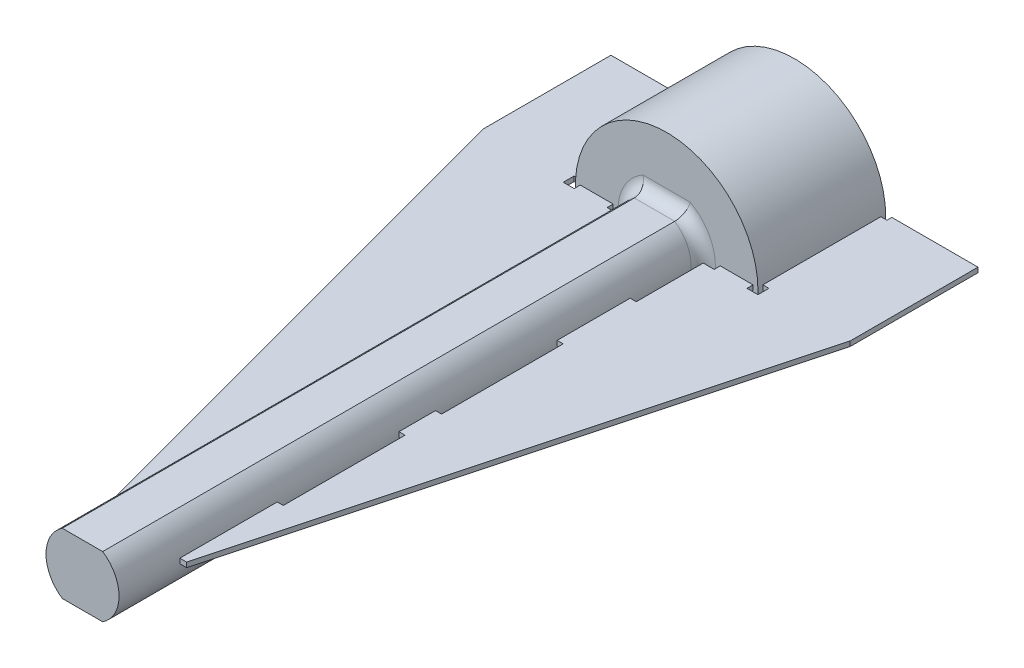
SolidWorks part; units mm, degrees
ref_plane "Front Plane" through (0, 0, 0) normal (0, 0, 1) x (1, 0, 0)
ref_plane "Top Plane" through (0, 0, 0) normal (0, 1, 0) x (1, 0, 0)
ref_plane "Right Plane" through (0, 0, 0) normal (1, 0, 0) x (0, 0, -1)
sketch "Sketch2" plane through (0, 0, 0) normal (0, 0, 1) x (1, 0, 0)
  arc A0 (-181.5583, 16.7096) -> (-181.559, 16.708) centre (-180.7258, 16.3677) ccw
  arc A1 (-181.559, 16.708) -> (-181.7515, 15.4803) centre (-179.0594, 15.6871) ccw
  arc A2 (-181.7515, 15.4803) -> (-180.9711, 14.942) centre (-178.5779, 19.2465) ccw
  arc A3 (-180.9711, 14.942) -> (-179.8919, 15.5581) centre (-181.7341, 17.532) ccw
  arc A4 (-179.8919, 15.5581) -> (-179.8906, 15.5593) centre (-180.506, 16.216) ccw
  arc A5 (-179.8906, 15.5593) -> (-179.8906, 15.5593) centre (-179.8906, 15.5593) cw
  arc A6 (-179.8906, 15.5593) -> (-179.8906, 15.5593) centre (-179.8906, 15.5593) ccw
  arc A7 (-179.8906, 15.5593) -> (-179.8906, 15.5593) centre (-179.8906, 15.5593) cw
  arc A8 (-179.8906, 15.5593) -> (-179.8904, 15.5575) centre (-178.9987, 15.6794) ccw
  arc A9 (-179.8904, 15.5575) -> (-179.4433, 14.3981) centre (-177.2152, 15.9232) ccw
  arc A10 (-179.4433, 14.3981) -> (-178.4982, 14.3221) centre (-178.5779, 19.2465) ccw
  arc A11 (-178.4982, 14.3221) -> (-177.8717, 15.3952) centre (-180.454, 16.1836) ccw
  arc A12 (-177.8717, 15.3952) -> (-177.8711, 15.3969) centre (-178.7324, 15.658) ccw
  arc A13 (-177.8711, 15.3969) -> (-177.8711, 15.3969) centre (-177.8711, 15.3969) cw
  arc A14 (-177.8711, 15.3969) -> (-177.8711, 15.3969) centre (-177.8711, 15.3969) ccw
  arc A15 (-177.8711, 15.3969) -> (-177.8711, 15.3969) centre (-177.8711, 15.3969) cw
  arc A16 (-177.8711, 15.3969) -> (-177.87, 15.3955) centre (-177.1587, 15.9469) ccw
  arc A17 (-177.87, 15.3955) -> (-176.9031, 14.615) centre (-175.7362, 17.0498) ccw
  arc A18 (-176.9031, 14.615) -> (-176.0467, 15.0217) centre (-178.5779, 19.2465) ccw
  arc A19 (-176.0467, 15.0217) -> (-176.0406, 16.2643) centre (-178.6712, 15.6559) ccw
  arc A20 (-176.0406, 16.2643) -> (-176.0411, 16.2661) centre (-176.9175, 16.0615) ccw
  arc A21 (-176.0411, 16.2661) -> (-176.0411, 16.2661) centre (-176.0411, 16.2661) cw
  arc A22 (-176.0411, 16.2661) -> (-176.0411, 16.2661) centre (-176.0411, 16.2661) ccw
  arc A23 (-176.0411, 16.2661) -> (-176.0411, 16.2661) centre (-176.0411, 16.2661) cw
  arc A24 (-176.0411, 16.2661) -> (-176.0394, 16.2654) centre (-175.6991, 17.0986) ccw
  arc A25 (-176.0394, 16.2654) -> (-174.8118, 16.0729) centre (-175.0185, 18.765) ccw
  arc A26 (-174.8118, 16.0729) -> (-174.2735, 16.8533) centre (-178.5779, 19.2465) ccw
  arc A27 (-174.2735, 16.8533) -> (-174.8895, 17.9325) centre (-176.8634, 16.0903) ccw
  arc A28 (-174.8895, 17.9325) -> (-174.8907, 17.9338) centre (-175.5475, 17.3184) ccw
  arc A29 (-174.8907, 17.9338) -> (-174.8907, 17.9338) centre (-174.8907, 17.9338) cw
  arc A30 (-174.8907, 17.9338) -> (-174.8907, 17.9338) centre (-174.8907, 17.9338) ccw
  arc A31 (-174.8907, 17.9338) -> (-174.8907, 17.9338) centre (-174.8907, 17.9338) cw
  arc A32 (-174.8907, 17.9338) -> (-174.8889, 17.9341) centre (-175.0108, 18.8258) ccw
  arc A33 (-174.8889, 17.9341) -> (-173.7295, 18.3812) centre (-175.2546, 20.6092) ccw
  arc A34 (-173.7295, 18.3812) -> (-173.6536, 19.3262) centre (-178.5779, 19.2465) ccw
  arc A35 (-173.6536, 19.3262) -> (-174.7267, 19.9528) centre (-175.515, 17.3704) ccw
  arc A36 (-174.7267, 19.9528) -> (-174.7284, 19.9533) centre (-174.9894, 19.092) ccw
  arc A37 (-174.7284, 19.9533) -> (-174.7284, 19.9533) centre (-174.7284, 19.9533) cw
  arc A38 (-174.7284, 19.9533) -> (-174.7284, 19.9533) centre (-174.7284, 19.9533) ccw
  arc A39 (-174.7284, 19.9533) -> (-174.7284, 19.9533) centre (-174.7284, 19.9533) cw
  arc A40 (-174.7284, 19.9533) -> (-174.7269, 19.9544) centre (-175.2784, 20.6657) ccw
  arc A41 (-174.7269, 19.9544) -> (-173.9464, 20.9213) centre (-176.3812, 22.0882) ccw
  arc A42 (-173.9464, 20.9213) -> (-174.3531, 21.7777) centre (-178.5779, 19.2465) ccw
  arc A43 (-174.3531, 21.7777) -> (-175.5958, 21.7838) centre (-174.9873, 19.1532) ccw
  arc A44 (-175.5958, 21.7838) -> (-175.5975, 21.7834) centre (-175.3929, 20.9069) ccw
  arc A45 (-175.5975, 21.7834) -> (-175.5975, 21.7834) centre (-175.5975, 21.7834) cw
  arc A46 (-175.5975, 21.7834) -> (-175.5975, 21.7834) centre (-175.5975, 21.7834) ccw
  arc A47 (-175.5975, 21.7834) -> (-175.5975, 21.7834) centre (-175.5975, 21.7834) cw
  arc A48 (-175.5975, 21.7834) -> (-175.5968, 21.785) centre (-176.43, 22.1253) ccw
  arc A49 (-175.5968, 21.785) -> (-175.4043, 23.0126) centre (-178.0964, 22.8059) ccw
  arc A50 (-175.4043, 23.0126) -> (-176.1848, 23.551) centre (-178.5779, 19.2465) ccw
  arc A51 (-176.1848, 23.551) -> (-177.2639, 22.9349) centre (-175.4217, 20.961) ccw
  arc A52 (-177.2639, 22.9349) -> (-177.2652, 22.9337) centre (-176.6499, 22.277) ccw
  arc A53 (-177.2652, 22.9337) -> (-177.2652, 22.9337) centre (-177.2652, 22.9337) cw
  arc A54 (-177.2652, 22.9337) -> (-177.2652, 22.9337) centre (-177.2652, 22.9337) ccw
  arc A55 (-177.2652, 22.9337) -> (-177.2652, 22.9337) centre (-177.2652, 22.9337) cw
  arc A56 (-177.2652, 22.9337) -> (-177.2655, 22.9355) centre (-178.1572, 22.8136) ccw
  arc A57 (-177.2655, 22.9355) -> (-177.7126, 24.0949) centre (-179.9406, 22.5698) ccw
  arc A58 (-177.7126, 24.0949) -> (-178.6576, 24.1708) centre (-178.5779, 19.2465) ccw
  arc A59 (-178.6576, 24.1708) -> (-179.2842, 23.0978) centre (-176.7018, 22.3094) ccw
  arc A60 (-179.2842, 23.0978) -> (-179.2847, 23.096) centre (-178.4234, 22.835) ccw
  arc A61 (-179.2847, 23.096) -> (-179.2847, 23.096) centre (-179.2847, 23.096) cw
  arc A62 (-179.2847, 23.096) -> (-179.2847, 23.096) centre (-179.2847, 23.096) ccw
  arc A63 (-179.2847, 23.096) -> (-179.2847, 23.096) centre (-179.2847, 23.096) cw
  arc A64 (-179.2847, 23.096) -> (-179.2858, 23.0975) centre (-179.9971, 22.546) ccw
  arc A65 (-179.2858, 23.0975) -> (-180.2527, 23.878) centre (-181.4197, 21.4432) ccw
  arc A66 (-180.2527, 23.878) -> (-181.1091, 23.4713) centre (-178.5779, 19.2465) ccw
  arc A67 (-181.1091, 23.4713) -> (-181.1152, 22.2287) centre (-178.4846, 22.8371) ccw
  arc A68 (-181.1152, 22.2287) -> (-181.1148, 22.2269) centre (-180.2383, 22.4315) ccw
  arc A69 (-181.1148, 22.2269) -> (-181.1148, 22.2269) centre (-181.1148, 22.2269) cw
  arc A70 (-181.1148, 22.2269) -> (-181.1148, 22.2269) centre (-181.1148, 22.2269) ccw
  arc A71 (-181.1148, 22.2269) -> (-181.1148, 22.2269) centre (-181.1148, 22.2269) cw
  arc A72 (-181.1148, 22.2269) -> (-181.1165, 22.2276) centre (-181.4567, 21.3944) ccw
  arc A73 (-181.1165, 22.2276) -> (-182.3441, 22.4201) centre (-182.1373, 19.728) ccw
  arc A74 (-182.3441, 22.4201) -> (-182.8824, 21.6397) centre (-178.5779, 19.2465) ccw
  arc A75 (-182.8824, 21.6397) -> (-182.2664, 20.5605) centre (-180.2924, 22.4027) ccw
  arc A76 (-182.2664, 20.5605) -> (-182.2651, 20.5592) centre (-181.6084, 21.1746) ccw
  arc A77 (-182.2651, 20.5592) -> (-182.2651, 20.5592) centre (-182.2651, 20.5592) cw
  arc A78 (-182.2651, 20.5592) -> (-182.2651, 20.5592) centre (-182.2651, 20.5592) ccw
  arc A79 (-182.2651, 20.5592) -> (-182.2651, 20.5592) centre (-182.2651, 20.5592) cw
  arc A80 (-182.2651, 20.5592) -> (-182.2669, 20.5589) centre (-182.145, 19.6672) ccw
  arc A81 (-182.2669, 20.5589) -> (-183.4263, 20.1118) centre (-181.9012, 17.8838) ccw
  arc A82 (-183.4263, 20.1118) -> (-183.5023, 19.1668) centre (-178.5779, 19.2465) ccw
  arc A83 (-183.5023, 19.1668) -> (-182.4292, 18.5402) centre (-181.6408, 21.1226) ccw
  arc A84 (-182.4292, 18.5402) -> (-182.4275, 18.5397) centre (-182.1664, 19.401) ccw
  arc A85 (-182.4275, 18.5397) -> (-182.4275, 18.5397) centre (-182.4275, 18.5397) cw
  arc A86 (-182.4275, 18.5397) -> (-182.4275, 18.5397) centre (-182.4275, 18.5397) ccw
  arc A87 (-182.4275, 18.5397) -> (-182.4275, 18.5397) centre (-182.4275, 18.5397) cw
  arc A88 (-182.4275, 18.5397) -> (-182.4289, 18.5386) centre (-181.8775, 17.8273) ccw
  arc A89 (-182.4289, 18.5386) -> (-183.2094, 17.5717) centre (-180.7746, 16.4047) ccw
  arc A90 (-183.2094, 17.5717) -> (-182.8027, 16.7153) centre (-178.5779, 19.2465) ccw
  arc A91 (-182.8027, 16.7153) -> (-181.5601, 16.7092) centre (-182.1685, 19.3398) ccw
  arc A92 (-181.5601, 16.7092) -> (-181.5583, 16.7096) centre (-181.7629, 17.5861) ccw
  arc A93 (-181.5583, 16.7096) -> (-181.5583, 16.7096) centre (-181.5583, 16.7096) cw
  arc A94 (-181.5583, 16.7096) -> (-181.5583, 16.7096) centre (-181.5583, 16.7096) ccw
  arc A95 (-181.5583, 16.7096) -> (-181.5583, 16.7096) centre (-181.5583, 16.7096) cw
  arc A96 (-180.9248, 16.8264) -> (-181.1887, 16.5567) centre (-180.7258, 16.3677) ccw
  arc A97 (-181.1887, 16.5567) -> (-181.3594, 15.6773) centre (-179.0594, 15.6871) ccw
  arc A98 (-181.3594, 15.6773) -> (-180.9262, 15.3785) centre (-178.5779, 19.2465) ccw
  arc A99 (-180.9262, 15.3785) -> (-180.1648, 15.8505) centre (-181.7341, 17.532) ccw
  arc A100 (-180.1648, 15.8505) -> (-180.0065, 16.193) centre (-180.506, 16.216) ccw
  arc A101 (-179.7323, 16.3694) -> (-180.0065, 16.193) centre (-179.8067, 16.1838) ccw
  arc A102 (-179.7323, 16.3694) -> (-179.5014, 16.2872) centre (-178.5779, 19.2465) ccw
  arc A103 (-179.4003, 15.9772) -> (-179.5014, 16.2872) centre (-179.561, 16.0963) ccw
  arc A104 (-179.4003, 15.9772) -> (-179.494, 15.6117) centre (-178.9987, 15.6794) ccw
  arc A105 (-179.494, 15.6117) -> (-179.2022, 14.7648) centre (-177.2152, 15.9232) ccw
  arc A106 (-179.2022, 14.7648) -> (-178.6776, 14.7226) centre (-178.5779, 19.2465) ccw
  arc A107 (-178.6776, 14.7226) -> (-178.2542, 15.512) centre (-180.454, 16.1836) ccw
  arc A108 (-178.2542, 15.512) -> (-178.2884, 15.8878) centre (-178.7324, 15.658) ccw
  arc A109 (-178.1391, 16.1777) -> (-178.2884, 15.8878) centre (-178.1108, 15.9797) ccw
  arc A110 (-178.1391, 16.1777) -> (-177.898, 16.222) centre (-178.5779, 19.2465) ccw
  arc A111 (-177.6555, 16.004) -> (-177.898, 16.222) centre (-177.8542, 16.0268) ccw
  arc A112 (-177.6555, 16.004) -> (-177.5539, 15.6406) centre (-177.1587, 15.9469) ccw
  arc A113 (-177.5539, 15.6406) -> (-176.8777, 15.0531) centre (-175.7362, 17.0498) ccw
  arc A114 (-176.8777, 15.0531) -> (-176.4023, 15.2788) centre (-178.5779, 19.2465) ccw
  arc A115 (-176.4023, 15.2788) -> (-176.4304, 16.1742) centre (-178.6712, 15.6559) ccw
  arc A116 (-176.4304, 16.1742) -> (-176.6478, 16.4826) centre (-176.9175, 16.0615) ccw
  arc A117 (-176.6635, 16.8083) -> (-176.6478, 16.4826) centre (-176.54, 16.651) ccw
  arc A118 (-176.6635, 16.8083) -> (-176.4769, 16.9671) centre (-178.5779, 19.2465) ccw
  arc A119 (-176.1578, 16.8996) -> (-176.4769, 16.9671) centre (-176.3413, 16.8201) ccw
  arc A120 (-176.1578, 16.8996) -> (-175.8881, 16.6357) centre (-175.6991, 17.0986) ccw
  arc A121 (-175.8881, 16.6357) -> (-175.0088, 16.465) centre (-175.0185, 18.765) ccw
  arc A122 (-175.0088, 16.465) -> (-174.71, 16.8982) centre (-178.5779, 19.2465) ccw
  arc A123 (-174.71, 16.8982) -> (-175.1819, 17.6596) centre (-176.8634, 16.0903) ccw
  arc A124 (-175.1819, 17.6596) -> (-175.5244, 17.8179) centre (-175.5475, 17.3184) ccw
  arc A125 (-175.7009, 18.0922) -> (-175.5244, 17.8179) centre (-175.5152, 18.0177) ccw
  arc A126 (-175.7009, 18.0922) -> (-175.6187, 18.323) centre (-178.5779, 19.2465) ccw
  arc A127 (-175.3086, 18.4241) -> (-175.6187, 18.323) centre (-175.4277, 18.2635) ccw
  arc A128 (-175.3086, 18.4241) -> (-174.9431, 18.3304) centre (-175.0108, 18.8258) ccw
  arc A129 (-174.9431, 18.3304) -> (-174.0962, 18.6222) centre (-175.2546, 20.6092) ccw
  arc A130 (-174.0962, 18.6222) -> (-174.054, 19.1468) centre (-178.5779, 19.2465) ccw
  arc A131 (-174.054, 19.1468) -> (-174.8434, 19.5702) centre (-175.515, 17.3704) ccw
  arc A132 (-174.8434, 19.5702) -> (-175.2192, 19.536) centre (-174.9894, 19.092) ccw
  arc A133 (-175.5091, 19.6853) -> (-175.2192, 19.536) centre (-175.3112, 19.7137) ccw
  arc A134 (-175.5091, 19.6853) -> (-175.5534, 19.9264) centre (-178.5779, 19.2465) ccw
  arc A135 (-175.3354, 20.1689) -> (-175.5534, 19.9264) centre (-175.3583, 19.9702) ccw
  arc A136 (-175.3354, 20.1689) -> (-174.972, 20.2705) centre (-175.2784, 20.6657) ccw
  arc A137 (-174.972, 20.2705) -> (-174.3845, 20.9467) centre (-176.3812, 22.0882) ccw
  arc A138 (-174.3845, 20.9467) -> (-174.6103, 21.4221) centre (-178.5779, 19.2465) ccw
  arc A139 (-174.6103, 21.4221) -> (-175.5056, 21.3941) centre (-174.9873, 19.1532) ccw
  arc A140 (-175.5056, 21.3941) -> (-175.814, 21.1766) centre (-175.3929, 20.9069) ccw
  arc A141 (-176.1397, 21.1609) -> (-175.814, 21.1766) centre (-175.9824, 21.2845) ccw
  arc A142 (-176.1397, 21.1609) -> (-176.2986, 21.3476) centre (-178.5779, 19.2465) ccw
  arc A143 (-176.2311, 21.6666) -> (-176.2986, 21.3476) centre (-176.1515, 21.4831) ccw
  arc A144 (-176.2311, 21.6666) -> (-175.9671, 21.9363) centre (-176.43, 22.1253) ccw
  arc A145 (-175.9671, 21.9363) -> (-175.7964, 22.8156) centre (-178.0964, 22.8059) ccw
  arc A146 (-175.7964, 22.8156) -> (-176.2296, 23.1145) centre (-178.5779, 19.2465) ccw
  arc A147 (-176.2296, 23.1145) -> (-176.991, 22.6425) centre (-175.4217, 20.961) ccw
  arc A148 (-176.991, 22.6425) -> (-177.1493, 22.3) centre (-176.6499, 22.277) ccw
  arc A149 (-177.4236, 22.1236) -> (-177.1493, 22.3) centre (-177.3491, 22.3092) ccw
  arc A150 (-177.4236, 22.1236) -> (-177.6545, 22.2058) centre (-178.5779, 19.2465) ccw
  arc A151 (-177.7555, 22.5158) -> (-177.6545, 22.2058) centre (-177.5949, 22.3967) ccw
  arc A152 (-177.7555, 22.5158) -> (-177.6618, 22.8813) centre (-178.1572, 22.8136) ccw
  arc A153 (-177.6618, 22.8813) -> (-177.9536, 23.7282) centre (-179.9406, 22.5698) ccw
  arc A154 (-177.9536, 23.7282) -> (-178.4782, 23.7704) centre (-178.5779, 19.2465) ccw
  arc A155 (-178.4782, 23.7704) -> (-178.9016, 22.981) centre (-176.7018, 22.3094) ccw
  arc A156 (-178.9016, 22.981) -> (-178.8675, 22.6052) centre (-178.4234, 22.835) ccw
  arc A157 (-179.0168, 22.3153) -> (-178.8675, 22.6052) centre (-179.0451, 22.5133) ccw
  arc A158 (-179.0168, 22.3153) -> (-179.2578, 22.271) centre (-178.5779, 19.2465) ccw
  arc A159 (-179.5004, 22.489) -> (-179.2578, 22.271) centre (-179.3017, 22.4661) ccw
  arc A160 (-179.5004, 22.489) -> (-179.6019, 22.8524) centre (-179.9971, 22.546) ccw
  arc A161 (-179.6019, 22.8524) -> (-180.2781, 23.4399) centre (-181.4197, 21.4432) ccw
  arc A162 (-180.2781, 23.4399) -> (-180.7535, 23.2142) centre (-178.5779, 19.2465) ccw
  arc A163 (-180.7535, 23.2142) -> (-180.7255, 22.3188) centre (-178.4846, 22.8371) ccw
  arc A164 (-180.7255, 22.3188) -> (-180.508, 22.0104) centre (-180.2383, 22.4315) ccw
  arc A165 (-180.4924, 21.6847) -> (-180.508, 22.0104) centre (-180.6159, 21.842) ccw
  arc A166 (-180.4924, 21.6847) -> (-180.679, 21.5259) centre (-178.5779, 19.2465) ccw
  arc A167 (-180.998, 21.5933) -> (-180.679, 21.5259) centre (-180.8145, 21.6729) ccw
  arc A168 (-180.998, 21.5933) -> (-181.2677, 21.8573) centre (-181.4567, 21.3944) ccw
  arc A169 (-181.2677, 21.8573) -> (-182.1471, 22.028) centre (-182.1373, 19.728) ccw
  arc A170 (-182.1471, 22.028) -> (-182.4459, 21.5948) centre (-178.5779, 19.2465) ccw
  arc A171 (-182.4459, 21.5948) -> (-181.9739, 20.8334) centre (-180.2924, 22.4027) ccw
  arc A172 (-181.9739, 20.8334) -> (-181.6314, 20.6751) centre (-181.6084, 21.1746) ccw
  arc A173 (-181.455, 20.4008) -> (-181.6314, 20.6751) centre (-181.6406, 20.4753) ccw
  arc A174 (-181.455, 20.4008) -> (-181.5372, 20.17) centre (-178.5779, 19.2465) ccw
  arc A175 (-181.8472, 20.0689) -> (-181.5372, 20.17) centre (-181.7281, 20.2295) ccw
  arc A176 (-181.8472, 20.0689) -> (-182.2127, 20.1626) centre (-182.145, 19.6672) ccw
  arc A177 (-182.2127, 20.1626) -> (-183.0597, 19.8708) centre (-181.9012, 17.8838) ccw
  arc A178 (-183.0597, 19.8708) -> (-183.1018, 19.3462) centre (-178.5779, 19.2465) ccw
  arc A179 (-183.1018, 19.3462) -> (-182.3124, 18.9228) centre (-181.6408, 21.1226) ccw
  arc A180 (-182.3124, 18.9228) -> (-181.9366, 18.9569) centre (-182.1664, 19.401) ccw
  arc A181 (-181.6467, 18.8076) -> (-181.9366, 18.9569) centre (-181.8447, 18.7793) ccw
  arc A182 (-181.6467, 18.8076) -> (-181.6024, 18.5666) centre (-178.5779, 19.2465) ccw
  arc A183 (-181.8204, 18.324) -> (-181.6024, 18.5666) centre (-181.7976, 18.5227) ccw
  arc A184 (-181.8204, 18.324) -> (-182.1838, 18.2225) centre (-181.8775, 17.8273) ccw
  arc A185 (-182.1838, 18.2225) -> (-182.7714, 17.5463) centre (-180.7746, 16.4047) ccw
  arc A186 (-182.7714, 17.5463) -> (-182.5456, 17.0709) centre (-178.5779, 19.2465) ccw
  arc A187 (-182.5456, 17.0709) -> (-181.6502, 17.0989) centre (-182.1685, 19.3398) ccw
  arc A188 (-181.6502, 17.0989) -> (-181.3419, 17.3164) centre (-181.7629, 17.5861) ccw
  arc A189 (-181.0161, 17.332) -> (-181.3419, 17.3164) centre (-181.1734, 17.2085) ccw
  arc A190 (-181.0161, 17.332) -> (-180.8573, 17.1454) centre (-178.5779, 19.2465) ccw
  arc A191 (-180.9248, 16.8264) -> (-180.8573, 17.1454) centre (-181.0043, 17.0099) ccw
  arc A192 (-180.9248, 16.8264) -> (-181.1887, 16.5567) centre (-180.7258, 16.3677) ccw construction
  arc A193 (-181.1887, 16.5567) -> (-181.3594, 15.6773) centre (-179.0594, 15.6871) ccw construction
  arc A194 (-181.3594, 15.6773) -> (-180.9262, 15.3785) centre (-178.5779, 19.2465) ccw construction
  arc A195 (-180.9262, 15.3785) -> (-180.1648, 15.8505) centre (-181.7341, 17.532) ccw construction
  arc A196 (-180.1648, 15.8505) -> (-180.0065, 16.193) centre (-180.506, 16.216) ccw construction
  arc A197 (-179.7323, 16.3694) -> (-180.0065, 16.193) centre (-179.8067, 16.1838) ccw construction
  arc A198 (-179.7323, 16.3694) -> (-179.5014, 16.2872) centre (-178.5779, 19.2465) ccw construction
  arc A199 (-179.4003, 15.9772) -> (-179.5014, 16.2872) centre (-179.561, 16.0963) ccw construction
  arc A200 (-179.4003, 15.9772) -> (-179.494, 15.6117) centre (-178.9987, 15.6794) ccw construction
  arc A201 (-179.494, 15.6117) -> (-179.2022, 14.7648) centre (-177.2152, 15.9232) ccw construction
  arc A202 (-179.2022, 14.7648) -> (-178.6776, 14.7226) centre (-178.5779, 19.2465) ccw construction
  arc A203 (-178.6776, 14.7226) -> (-178.2542, 15.512) centre (-180.454, 16.1836) ccw construction
  arc A204 (-178.2542, 15.512) -> (-178.2884, 15.8878) centre (-178.7324, 15.658) ccw construction
  arc A205 (-178.1391, 16.1777) -> (-178.2884, 15.8878) centre (-178.1108, 15.9797) ccw construction
  arc A206 (-178.1391, 16.1777) -> (-177.898, 16.222) centre (-178.5779, 19.2465) ccw construction
  arc A207 (-177.6555, 16.004) -> (-177.898, 16.222) centre (-177.8542, 16.0268) ccw construction
  arc A208 (-177.6555, 16.004) -> (-177.5539, 15.6406) centre (-177.1587, 15.9469) ccw construction
  arc A209 (-177.5539, 15.6406) -> (-176.8777, 15.0531) centre (-175.7362, 17.0498) ccw construction
  arc A210 (-176.8777, 15.0531) -> (-176.4023, 15.2788) centre (-178.5779, 19.2465) ccw construction
  arc A211 (-176.4023, 15.2788) -> (-176.4304, 16.1742) centre (-178.6712, 15.6559) ccw construction
  arc A212 (-176.4304, 16.1742) -> (-176.6478, 16.4826) centre (-176.9175, 16.0615) ccw construction
  arc A213 (-176.6635, 16.8083) -> (-176.6478, 16.4826) centre (-176.54, 16.651) ccw construction
  arc A214 (-176.6635, 16.8083) -> (-176.4769, 16.9671) centre (-178.5779, 19.2465) ccw construction
  arc A215 (-176.1578, 16.8996) -> (-176.4769, 16.9671) centre (-176.3413, 16.8201) ccw construction
  arc A216 (-176.1578, 16.8996) -> (-175.8881, 16.6357) centre (-175.6991, 17.0986) ccw construction
  arc A217 (-175.8881, 16.6357) -> (-175.0088, 16.465) centre (-175.0185, 18.765) ccw construction
  arc A218 (-175.0088, 16.465) -> (-174.71, 16.8982) centre (-178.5779, 19.2465) ccw construction
  arc A219 (-174.71, 16.8982) -> (-175.1819, 17.6596) centre (-176.8634, 16.0903) ccw construction
  arc A220 (-175.1819, 17.6596) -> (-175.5244, 17.8179) centre (-175.5475, 17.3184) ccw construction
  arc A221 (-175.7009, 18.0922) -> (-175.5244, 17.8179) centre (-175.5152, 18.0177) ccw construction
  arc A222 (-175.7009, 18.0922) -> (-175.6187, 18.323) centre (-178.5779, 19.2465) ccw construction
  arc A223 (-175.3086, 18.4241) -> (-175.6187, 18.323) centre (-175.4277, 18.2635) ccw construction
  arc A224 (-175.3086, 18.4241) -> (-174.9431, 18.3304) centre (-175.0108, 18.8258) ccw construction
  arc A225 (-174.9431, 18.3304) -> (-174.0962, 18.6222) centre (-175.2546, 20.6092) ccw construction
  arc A226 (-174.0962, 18.6222) -> (-174.054, 19.1468) centre (-178.5779, 19.2465) ccw construction
  arc A227 (-174.054, 19.1468) -> (-174.8434, 19.5702) centre (-175.515, 17.3704) ccw construction
  arc A228 (-174.8434, 19.5702) -> (-175.2192, 19.536) centre (-174.9894, 19.092) ccw construction
  arc A229 (-175.5091, 19.6853) -> (-175.2192, 19.536) centre (-175.3112, 19.7137) ccw construction
  arc A230 (-175.5091, 19.6853) -> (-175.5534, 19.9264) centre (-178.5779, 19.2465) ccw construction
  arc A231 (-175.3354, 20.1689) -> (-175.5534, 19.9264) centre (-175.3583, 19.9702) ccw construction
  arc A232 (-175.3354, 20.1689) -> (-174.972, 20.2705) centre (-175.2784, 20.6657) ccw construction
  arc A233 (-174.972, 20.2705) -> (-174.3845, 20.9467) centre (-176.3812, 22.0882) ccw construction
  arc A234 (-174.3845, 20.9467) -> (-174.6103, 21.4221) centre (-178.5779, 19.2465) ccw construction
  arc A235 (-174.6103, 21.4221) -> (-175.5056, 21.3941) centre (-174.9873, 19.1532) ccw construction
  arc A236 (-175.5056, 21.3941) -> (-175.814, 21.1766) centre (-175.3929, 20.9069) ccw construction
  arc A237 (-176.1397, 21.1609) -> (-175.814, 21.1766) centre (-175.9824, 21.2845) ccw construction
  arc A238 (-176.1397, 21.1609) -> (-176.2986, 21.3476) centre (-178.5779, 19.2465) ccw construction
  arc A239 (-176.2311, 21.6666) -> (-176.2986, 21.3476) centre (-176.1515, 21.4831) ccw construction
  arc A240 (-176.2311, 21.6666) -> (-175.9671, 21.9363) centre (-176.43, 22.1253) ccw construction
  arc A241 (-175.9671, 21.9363) -> (-175.7964, 22.8156) centre (-178.0964, 22.8059) ccw construction
  arc A242 (-175.7964, 22.8156) -> (-176.2296, 23.1145) centre (-178.5779, 19.2465) ccw construction
  arc A243 (-176.2296, 23.1145) -> (-176.991, 22.6425) centre (-175.4217, 20.961) ccw construction
  arc A244 (-176.991, 22.6425) -> (-177.1493, 22.3) centre (-176.6499, 22.277) ccw construction
  arc A245 (-177.4236, 22.1236) -> (-177.1493, 22.3) centre (-177.3491, 22.3092) ccw construction
  arc A246 (-177.4236, 22.1236) -> (-177.6545, 22.2058) centre (-178.5779, 19.2465) ccw construction
  arc A247 (-177.7555, 22.5158) -> (-177.6545, 22.2058) centre (-177.5949, 22.3967) ccw construction
  arc A248 (-177.7555, 22.5158) -> (-177.6618, 22.8813) centre (-178.1572, 22.8136) ccw construction
  arc A249 (-177.6618, 22.8813) -> (-177.9536, 23.7282) centre (-179.9406, 22.5698) ccw construction
  arc A250 (-177.9536, 23.7282) -> (-178.4782, 23.7704) centre (-178.5779, 19.2465) ccw construction
  arc A251 (-178.4782, 23.7704) -> (-178.9016, 22.981) centre (-176.7018, 22.3094) ccw construction
  arc A252 (-178.9016, 22.981) -> (-178.8675, 22.6052) centre (-178.4234, 22.835) ccw construction
  arc A253 (-179.0168, 22.3153) -> (-178.8675, 22.6052) centre (-179.0451, 22.5133) ccw construction
  arc A254 (-179.0168, 22.3153) -> (-179.2578, 22.271) centre (-178.5779, 19.2465) ccw construction
  arc A255 (-179.5004, 22.489) -> (-179.2578, 22.271) centre (-179.3017, 22.4661) ccw construction
  arc A256 (-179.5004, 22.489) -> (-179.6019, 22.8524) centre (-179.9971, 22.546) ccw construction
  arc A257 (-179.6019, 22.8524) -> (-180.2781, 23.4399) centre (-181.4197, 21.4432) ccw construction
  arc A258 (-180.2781, 23.4399) -> (-180.7535, 23.2142) centre (-178.5779, 19.2465) ccw construction
  arc A259 (-180.7535, 23.2142) -> (-180.7255, 22.3188) centre (-178.4846, 22.8371) ccw construction
  arc A260 (-180.7255, 22.3188) -> (-180.508, 22.0104) centre (-180.2383, 22.4315) ccw construction
  arc A261 (-180.4924, 21.6847) -> (-180.508, 22.0104) centre (-180.6159, 21.842) ccw construction
  arc A262 (-180.4924, 21.6847) -> (-180.679, 21.5259) centre (-178.5779, 19.2465) ccw construction
  arc A263 (-180.998, 21.5933) -> (-180.679, 21.5259) centre (-180.8145, 21.6729) ccw construction
  arc A264 (-180.998, 21.5933) -> (-181.2677, 21.8573) centre (-181.4567, 21.3944) ccw construction
  arc A265 (-181.2677, 21.8573) -> (-182.1471, 22.028) centre (-182.1373, 19.728) ccw construction
  arc A266 (-182.1471, 22.028) -> (-182.4459, 21.5948) centre (-178.5779, 19.2465) ccw construction
  arc A267 (-182.4459, 21.5948) -> (-181.9739, 20.8334) centre (-180.2924, 22.4027) ccw construction
  arc A268 (-181.9739, 20.8334) -> (-181.6314, 20.6751) centre (-181.6084, 21.1746) ccw construction
  arc A269 (-181.455, 20.4008) -> (-181.6314, 20.6751) centre (-181.6406, 20.4753) ccw construction
  arc A270 (-181.455, 20.4008) -> (-181.5372, 20.17) centre (-178.5779, 19.2465) ccw construction
  arc A271 (-181.8472, 20.0689) -> (-181.5372, 20.17) centre (-181.7281, 20.2295) ccw construction
  arc A272 (-181.8472, 20.0689) -> (-182.2127, 20.1626) centre (-182.145, 19.6672) ccw construction
  arc A273 (-182.2127, 20.1626) -> (-183.0597, 19.8708) centre (-181.9012, 17.8838) ccw construction
  arc A274 (-183.0597, 19.8708) -> (-183.1018, 19.3462) centre (-178.5779, 19.2465) ccw construction
  arc A275 (-183.1018, 19.3462) -> (-182.3124, 18.9228) centre (-181.6408, 21.1226) ccw construction
  arc A276 (-182.3124, 18.9228) -> (-181.9366, 18.9569) centre (-182.1664, 19.401) ccw construction
  arc A277 (-181.6467, 18.8076) -> (-181.9366, 18.9569) centre (-181.8447, 18.7793) ccw construction
  arc A278 (-181.6467, 18.8076) -> (-181.6024, 18.5666) centre (-178.5779, 19.2465) ccw construction
  arc A279 (-181.8204, 18.324) -> (-181.6024, 18.5666) centre (-181.7976, 18.5227) ccw construction
  arc A280 (-181.8204, 18.324) -> (-182.1838, 18.2225) centre (-181.8775, 17.8273) ccw construction
  arc A281 (-182.1838, 18.2225) -> (-182.7714, 17.5463) centre (-180.7746, 16.4047) ccw construction
  arc A282 (-182.7714, 17.5463) -> (-182.5456, 17.0709) centre (-178.5779, 19.2465) ccw construction
  arc A283 (-182.5456, 17.0709) -> (-181.6502, 17.0989) centre (-182.1685, 19.3398) ccw construction
  arc A284 (-181.6502, 17.0989) -> (-181.3419, 17.3164) centre (-181.7629, 17.5861) ccw construction
  arc A285 (-181.0161, 17.332) -> (-181.3419, 17.3164) centre (-181.1734, 17.2085) ccw construction
  arc A286 (-181.0161, 17.332) -> (-180.8573, 17.1454) centre (-178.5779, 19.2465) ccw construction
  arc A287 (-180.9248, 16.8264) -> (-180.8573, 17.1454) centre (-181.0043, 17.0099) ccw construction
  circle A288 centre (-178.5779, 19.2465) radius 7.5
  dimension "D3" = 15
  dimension "D1" = 0
  dimension "D2" = 0.4
extrude "Boss-Extrude1" add sketch "Sketch2" against normal offset from surface 0.5 and the other way offset from surface (4 mm away) 1
sketch "Sketch4" plane through (0, 0, 4) normal (0, 0, 1) x (1, 0, 0)
  circle A1 centre (-178.5779, 19.2465) radius 7.5
  circle A2 centre (-178.5779, 19.2465) radius 7.5
  dimension "D1" = 0
extrude "Boss-Extrude2" add sketch "Sketch4" along normal blind 1
sketch "Sketch6" plane through (0, 0, 5) normal (0, 0, 1) x (1, 0, 0)
  line L1 (-180.2362, 21.7465) -> (-176.9196, 21.7465)
  line L2 (-180.2362, 21.7465) -> (-180.2362, 16.7465) construction
  line L3 (-180.2362, 16.7465) -> (-176.9196, 16.7465)
  line L4 (-176.9196, 21.7465) -> (-176.9196, 16.7465) construction
  line L5 (-180.2362, 21.7465) -> (-176.9196, 16.7465) construction
  line L6 (-180.2362, 16.7465) -> (-176.9196, 21.7465) construction
  arc A0 (-180.2362, 21.7465) -> (-180.2362, 16.7465) centre (-178.5779, 19.2465) ccw
  arc A1 (-176.9196, 16.7465) -> (-176.9196, 21.7465) centre (-178.5779, 19.2465) ccw
  dimension "D1" = 6
  dimension "D2" = 2.5
extrude "Boss-Extrude3" add sketch "Sketch6" along normal blind 48
fillet "Fillet1" radius 1 4 edges at (-181.5779, 19.2465, 5) (-178.5779, 16.7465, 5) (-175.5779, 19.2465, 5) (-178.5779, 21.7465, 5)
ref_plane "Plane1" through (0, 19.2465, 0) normal (0, 1, 0) x (1, 0, 0)
sketch "Sketch7" plane through (0, 19.2465, 0) normal (0, 1, 0) x (1, 0, 0)
  line L1 (-182.0779, -5.5) -> (-182.0779, -11)
  line L2 (-182.1358, -48) -> (-193.6576, -5)
  line L3 (-186.5779, -5.5) -> (-185.6779, -5.5)
  line L5 (-171.0779, 5.5) -> (-186.0779, 5.5) construction
  line L6 (-186.5779, 5.5) -> (-193.6576, 5.5)
  line L7 (-186.5779, 5.5) -> (-186.5779, 5.1)
  line L9 (-193.6576, 5.5) -> (-193.6576, -5)
  line L10 (-186.0779, 5.5) -> (-186.0779, -5) construction
  line L11 (-186.0779, -5) -> (-171.0779, -5) construction
  line L12 (-181.5779, -6) -> (-181.5779, -53) construction
  line L13 (-186.5779, -4.6) -> (-186.5779, -5.5)
  line L14 (-186.5779, 5.1) -> (-186.0779, 5.1)
  line L16 (-186.5779, -4.6) -> (-186.0779, -4.6)
  line L17 (-186.0779, 5.1) -> (-186.0779, -4.6)
  line L19 (-185.6779, -5) -> (-182.9779, -5)
  line L20 (-185.6779, -5) -> (-185.6779, -5.5)
  line L22 (-182.9779, -5) -> (-182.9779, -5.5)
  line L23 (-182.0779, -11) -> (-181.5779, -11)
  line L25 (-182.0779, -17) -> (-181.5779, -17)
  line L26 (-181.5779, -11) -> (-181.5779, -17)
  line L27 (-182.0779, -27) -> (-181.5779, -27)
  line L29 (-182.0779, -30) -> (-181.5779, -30)
  line L30 (-181.5779, -27) -> (-181.5779, -30)
  line L31 (-182.0779, -40) -> (-181.5779, -40)
  line L33 (-182.1358, -48) -> (-181.5779, -48)
  line L34 (-181.5779, -40) -> (-181.5779, -48)
  line L39 (-182.9779, -5.5) -> (-182.0779, -5.5)
  line L40 (-182.0779, -17) -> (-182.0779, -27)
  line L41 (-182.0779, -30) -> (-182.0779, -40)
  line L43 (-180.2362, -6) -> (-181.5779, -6) construction
  line L44 (-182.5779, -5) -> (-180.5144, -5) construction
  line L45 (-176.9196, -53) -> (-180.2362, -53) construction
  line L46 (-178.5779, 5.5) -> (-178.5779, -53) construction
  line L47 (-175.02, -48) -> (-175.5779, -48)
  line L48 (-175.5779, -40) -> (-175.5779, -48)
  line L49 (-175.0779, -40) -> (-175.5779, -40)
  line L50 (-175.0779, -30) -> (-175.0779, -40)
  line L51 (-175.0779, -30) -> (-175.5779, -30)
  line L52 (-175.5779, -27) -> (-175.5779, -30)
  line L53 (-175.0779, -27) -> (-175.5779, -27)
  line L54 (-175.0779, -17) -> (-175.0779, -27)
  line L55 (-175.0779, -17) -> (-175.5779, -17)
  line L56 (-175.5779, -11) -> (-175.5779, -17)
  line L57 (-175.0779, -11) -> (-175.5779, -11)
  line L58 (-175.0779, -5.5) -> (-175.0779, -11)
  line L59 (-174.1779, -5.5) -> (-175.0779, -5.5)
  line L60 (-174.1779, -5) -> (-174.1779, -5.5)
  line L61 (-171.4779, -5) -> (-174.1779, -5)
  line L62 (-171.4779, -5) -> (-171.4779, -5.5)
  line L63 (-170.5779, -5.5) -> (-171.4779, -5.5)
  line L64 (-170.5779, -4.6) -> (-170.5779, -5.5)
  line L65 (-170.5779, -4.6) -> (-171.0779, -4.6)
  line L66 (-171.0779, 5.1) -> (-171.0779, -4.6)
  line L67 (-170.5779, 5.1) -> (-171.0779, 5.1)
  line L68 (-170.5779, 5.5) -> (-170.5779, 5.1)
  line L69 (-170.5779, 5.5) -> (-163.4982, 5.5)
  line L70 (-163.4982, 5.5) -> (-163.4982, -5)
  line L71 (-175.02, -48) -> (-163.4982, -5)
  arc A0 (-181.5779, -6) -> (-182.5779, -5) centre (-182.5779, -6) ccw construction
  dimension "D1" = 0.5
  dimension "D2" = 0.5
  dimension "D3" = 0.5
  dimension "D4" = 0.4
  dimension "D5" = 0.4
  dimension "D6" = 0.4
  dimension "D7" = 0.4
  dimension "D8" = 5
  dimension "D9" = 10
  dimension "D10" = 10
  dimension "D11" = 5
  dimension "D12" = 12
  dimension "D13" = 25
  dimension "D14" = 15
  dimension "D15" = 15
extrude "Boss-Extrude6" add sketch "Sketch7" along normal mid plane 0.4 separate body
